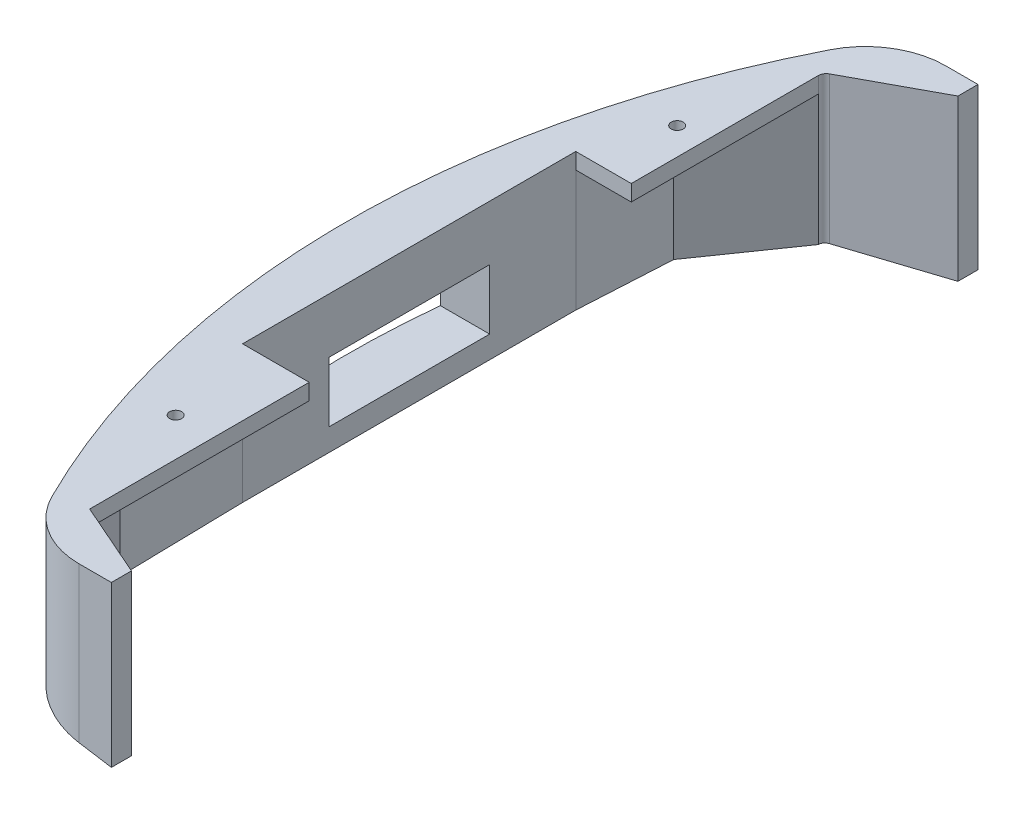
SolidWorks part; units mm, degrees
ref_plane "Front Plane" through (0, 0, 0) normal (0, 0, 1) x (1, 0, 0)
ref_plane "Top Plane" through (0, 0, 0) normal (0, 1, 0) x (1, 0, 0)
ref_plane "Right Plane" through (0, 0, 0) normal (1, 0, 0) x (0, 0, -1)
sketch "front_sketch" plane through (0, 0, 0) normal (0, 1, 0) x (1, 0, 0)
  line L4 (-94.9614, 124.4785) -> (-121.3453, 110.2345)
  line L10 (-122.6787, 107.9994) -> (-122.6787, 48.8108)
  line L24 (-94.9614, 130.8285) -> (-94.9614, 124.4785) construction
  line L25 (-94.9614, 124.4785) -> (-69.5614, 124.4785) construction
  line L28 (-95.6016, -142.8102) -> (-95.6016, -136.4602)
  line L29 (-95.6016, -136.4602) -> (-70.2016, -136.4602) construction
  line L34 (-122.6787, 48.8108) -> (-140.2508, 48.8108)
  line L36 (-140.2508, 48.8108) -> (-140.2508, -56.6452)
  line L43 (-140.2508, -56.6452) -> (-119.167, -56.6452)
  line L44 (-119.167, -56.6452) -> (-119.167, -126.1123)
  line L50 (-119.167, -126.1123) -> (-95.6016, -136.4602)
  line L129 (-94.9614, 130.8285) -> (-69.5614, 130.8285) construction
  line L130 (-94.9614, 130.8285) -> (-69.5614, 130.8285) construction
  line L225 (-95.5505, 130.8285) -> (-157.7358, 130.8285) construction
  line L248 (-94.9614, 130.8285) -> (-95.5505, 130.8285) construction
  line L254 (-94.9614, 130.8285) -> (-95.5505, 130.8285) construction
  line L257 (-94.9614, 130.8285) -> (-105.2412, 130.8285)
  line L258 (-95.5505, 130.8285) -> (-94.9614, 130.8285) construction
  line L259 (-95.6016, -142.8102) -> (-105.7982, -142.8102)
  line L260 (-94.9614, 124.4785) -> (-94.9614, 130.8285)
  line L261 (-94.9614, 130.8285) -> (-95.5505, 130.8285) construction
  line L263 (-95.6016, -142.8102) -> (-70.2016, -142.8102) construction
  line L264 (-95.6016, -142.8102) -> (-70.2016, -142.8102) construction
  line L267 (-97.1554, -142.8102) -> (-95.6016, -142.8102) construction
  line L294 (-94.9614, 130.8285) -> (-95.5505, 130.8285) construction
  line L295 (-157.7358, 130.8285) -> (-157.7358, -142.8102) construction
  line L296 (-157.7358, -142.8102) -> (-97.1554, -142.8102) construction
  line L297 (-95.5505, 130.8285) -> (-157.7358, 130.8285) construction
  arc A41 (-127.9188, 116.8691) -> (-128.5327, -128.7374) centre (116.7138, -6.5464) ccw
  arc A42 (-127.9188, 116.8691) -> (-105.2412, 130.8285) centre (-105.2412, 105.4285) cw
  arc A43 (-128.5327, -128.7374) -> (-105.7982, -142.8102) centre (-105.7982, -117.4102) ccw
  circle A44 centre (-131.2964, 71.9636) radius 1.905
  circle A45 centre (-131.2964, -86.7864) radius 1.905
  arc A48 (-122.6787, 107.9994) -> (-121.3453, 110.2345) centre (-120.1387, 107.9994) cw
  dimension "D12" = 25.4
  dimension "D14" = 25.4
  dimension "D30" = 3.81
  dimension "D4" = 2.54
  dimension "D19" = 6.35
  dimension "D27" = 10.2799
  dimension "D28" = 10.1966
extrude "Boss-Extrude1" add sketch "front_sketch" along normal blind 50.8
sketch "Sketch1" plane through (0, 50.8, 0) normal (0, 1, 0) x (1, 0, 0)
  line L0 (-122.6787, 48.8108) -> (-122.6787, 107.9994)
  line L1 (-122.6787, 107.9994) -> (-138.8333, 78.4051)
  line L2 (-138.8333, 78.4051) -> (-140.2508, 48.8108)
  line L3 (-140.2508, 48.8108) -> (-122.6787, 48.8108)
  line L4 (-119.167, -56.6452) -> (-140.2508, -56.6452)
  line L5 (-119.167, -56.6452) -> (-140.2508, -56.6452) construction
  line L6 (-140.2508, -56.6452) -> (-140.2508, 48.8108) construction
  line L7 (-140.2508, -56.6452) -> (-139.5421, -96.1925)
  line L8 (-139.5421, -96.1925) -> (-119.167, -126.1123)
  line L9 (-119.167, -126.1123) -> (-119.167, -56.6452) construction
  line L10 (-95.6016, -136.4602) -> (-119.167, -126.1123) construction
  line L11 (-119.167, -126.1123) -> (-119.167, -56.6452)
extrude "Cut-Extrude1" cut sketch "Sketch1" along normal blind 48.26 from offset 53.34 offset against normal yes
sketch "Sketch2" plane through (0, 0, 142.8102) normal (0, 0, 1) x (1, 0, 0)
  line L0 (-94.9614, 0) -> (-157.2871, 0)
  line L1 (-157.2871, 0) -> (-157.2871, 10.0565)
  line L2 (-157.2871, 50.8) -> (-157.2871, 0) construction
  line L3 (-157.2871, 10.0565) -> (-94.9614, 0)
extrude "Cut-Extrude2" cut sketch "Sketch2" against normal through all
sketch "Sketch3" plane through (-140.2508, 0, 0) normal (1, 0, 0) x (0, 0, -1)
  circle A0 centre (-17.3122, 23.9848) radius 3.175
  circle A1 centre (11.2741, 23.9848) radius 3.175
extrude "Cut-Extrude3" cut sketch "Sketch3" against normal through all
sketch "Sketch4" plane through (-140.2508, 0, 0) normal (1, 0, 0) x (0, 0, -1)
  line L1 (-29.2461, 33.4173) -> (21.5539, 33.4173)
  line L2 (-29.2461, 33.4173) -> (-29.2461, 14.3673)
  line L3 (-29.2461, 14.3673) -> (21.5539, 14.3673)
  line L4 (21.5539, 33.4173) -> (21.5539, 14.3673)
  dimension "D1" = 50.8
  dimension "D2" = 19.05
extrude "Cut-Extrude4" cut sketch "Sketch4" against normal blind 22.86
